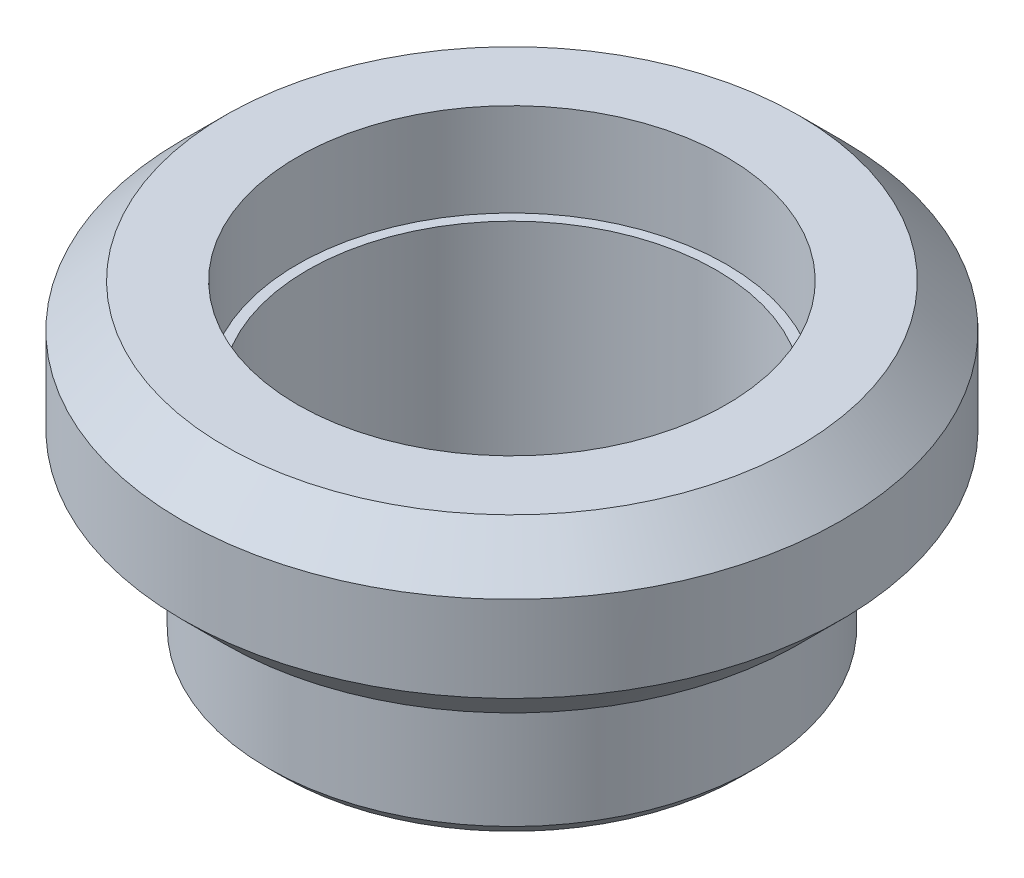
SolidWorks part; units mm, degrees
ref_plane "Front Plane" through (0, 0, 0) normal (0, 0, 1) x (1, 0, 0)
ref_plane "Top Plane" through (0, 0, 0) normal (0, 1, 0) x (1, 0, 0)
ref_plane "Right Plane" through (0, 0, 0) normal (1, 0, 0) x (0, 0, -1)
sketch "Sketch1" plane through (0, 0, 0) normal (0, 0, 1) x (1, 0, 0)
  line L0 (0, 0) -> (14.3, 0) construction
  line L4 (14.3, 0) -> (17.05, 0)
  line L5 (17.05, 10) -> (17.05, 0)
  line L6 (17.05, 10) -> (23.05, 10)
  line L8 (15, 22) -> (23.05, 22)
  line L9 (23.05, 10) -> (23.05, 22)
  line L12 (14.3, 15.5) -> (15, 15.5)
  line L13 (15, 22) -> (15, 15.5)
  line L14 (14.3, 15.5) -> (14.3, 0)
  point P7 (12.3545, 0)
  point P12 (19.109, 10.3186)
  point P13 (0, 0)
  point P15 (21.9777, 9)
  point P16 (19.2402, 9)
  point P17 (14.3, 10.5973)
  point P18 (19.2402, 9)
  dimension "D1" = 17.05
  dimension "D2" = 10
  dimension "D3" = 6
  dimension "D4" = 12
  dimension "D5" = 14.3
  dimension "D6" = 6.5
  dimension "D7" = 15
ref_axis "Axis1" through (0, 23.1, 0) along (0, -1, 0)
revolve "Revolve1" add sketch "Sketch1" angle 360 about axis through (0, 23.1, 0) along (0, -1, 0)
chamfer "Chamfer1" distance 3 angle 45 2 edges at (0, 10, 23.05) (0, 22, 23.05)
chamfer "Chamfer2" distance 1 angle 45 1 edges at (0, 0, 17.05)
